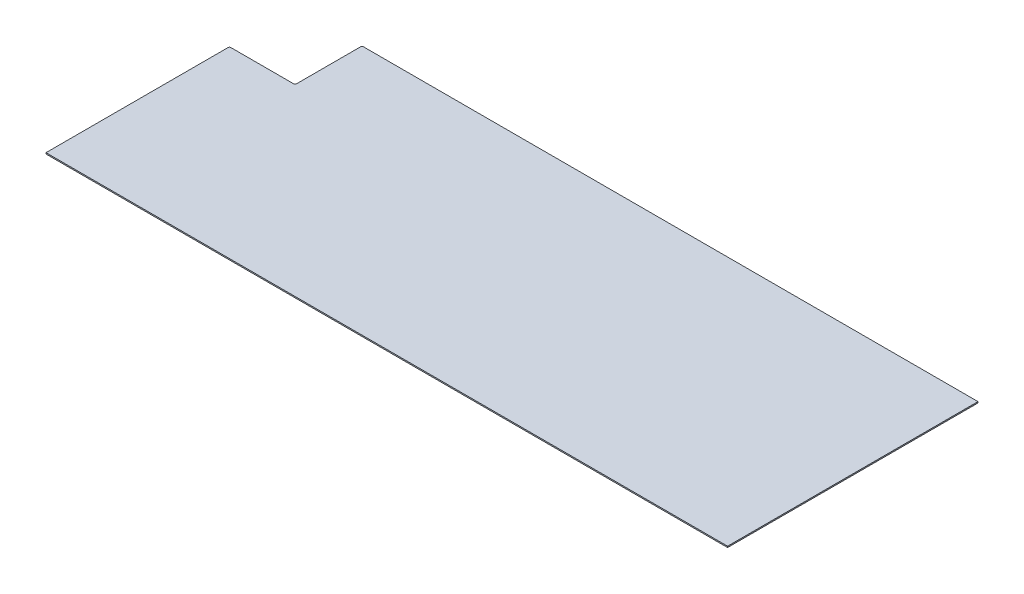
SolidWorks part; units mm, degrees
material "Pine"
ref_plane "Front Plane" through (0, 0, 0) normal (0, 0, 1) x (1, 0, 0)
ref_plane "Top Plane" through (0, 0, 0) normal (0, 1, 0) x (1, 0, 0)
ref_plane "Right Plane" through (0, 0, 0) normal (1, 0, 0) x (0, 0, -1)
sketch "Sketch1" plane through (0, 0, 0) normal (0, 1, 0) x (1, 0, 0)
  line L1 (0, 0) -> (1616.075, 0)
  line L2 (0, 0) -> (0, 431.8)
  line L3 (158.75, 593.725) -> (1616.075, 593.725)
  line L4 (1616.075, 0) -> (1616.075, 593.725)
  line L5 (3.175, 434.975) -> (152.4, 434.975)
  line L8 (155.575, 438.15) -> (155.575, 590.55)
  arc A0 (155.575, 590.55) -> (158.75, 593.725) centre (158.75, 590.55) cw
  arc A1 (155.575, 438.15) -> (152.4, 434.975) centre (152.4, 438.15) cw
  arc A2 (3.175, 434.975) -> (0, 431.8) centre (3.175, 431.8) ccw
  point P9 (155.575, 593.725)
  point P12 (155.575, 434.975)
  point P15 (0, 434.975)
  dimension "D5" = 3.175
  dimension "D1" = 434.975
  dimension "D2" = 155.575
  dimension "D3" = 158.75
  dimension "D4" = 1616.075
extrude "Boss-Extrude1" add sketch "Sketch1" along normal blind 2.921
